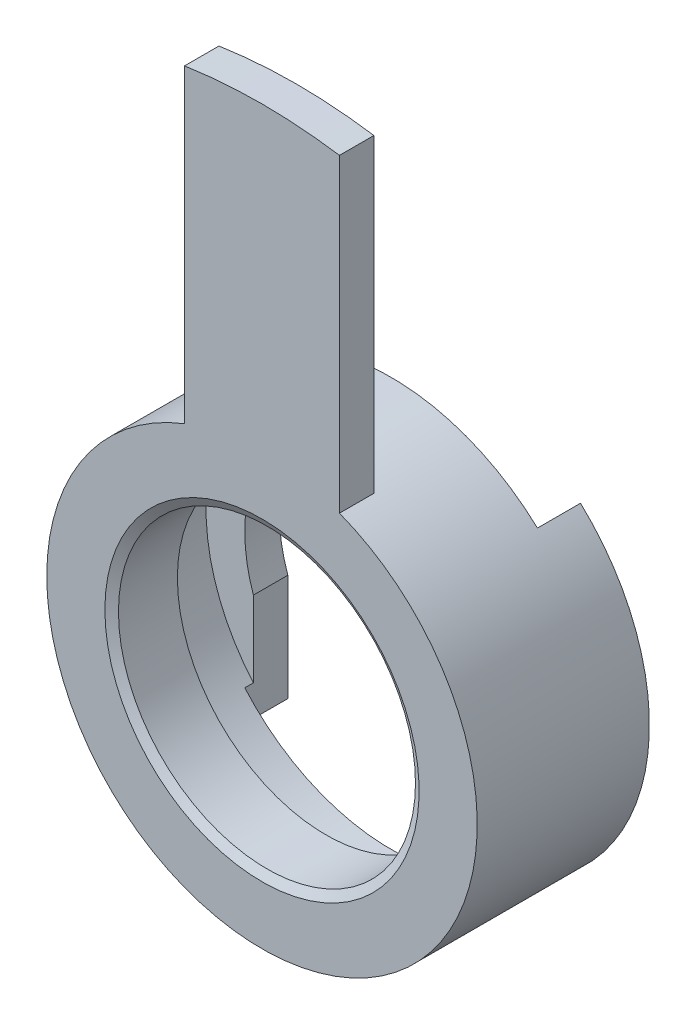
SolidWorks part; units mm, degrees
ref_plane "Спереди" through (0, 0, 0) normal (0, 0, 1) x (1, 0, 0)
ref_plane "Сверху" through (0, 0, 0) normal (0, 1, 0) x (1, 0, 0)
ref_plane "Справа" through (0, 0, 0) normal (1, 0, 0) x (0, 0, -1)
sketch "Эскиз1" plane through (0, 0, 0) normal (1, 0, 0) x (0, 0, -1)
  line L0 (0, 17.25) -> (0, 60)
  line L1 (0, 60) -> (4, 60)
  line L2 (4, 60) -> (4, 25)
  line L3 (4, 25) -> (20, 25)
  line L4 (20, 25) -> (20, 18)
  line L5 (20, 18) -> (16, 18)
  line L6 (16, 18) -> (16, 22.5)
  line L7 (16, 22.5) -> (8, 22.5)
  line L8 (8, 22.5) -> (8, 17.25)
  line L9 (8, 17.25) -> (0, 17.25)
  line L10 (0, 0) -> (25.7334, 0) construction
  dimension "D1" = 36
  dimension "D2" = 45
  dimension "D3" = 50
  dimension "D4" = 34.5
  dimension "D5" = 120
  dimension "D6" = 4
  dimension "D7" = 20
  dimension "D8" = 8
  dimension "D9" = 4
revolve "Повернуть1" add sketch "Эскиз1" angle 360 about L10
cosmetic thread "Условное изображение резьбы1" parameters "D2"=36
chamfer "Фаска1" distance 1 angle 30 2 edges at (17.25, 0, -8) (17.25, 0, 0)
sketch "Эскиз2" plane through (0, 0, -20) normal (0, 0, -1) x (-1, 0, 0)
  line L0 (-17, 18.3303) -> (-17, -18.3303)
  line L1 (17, 18.3303) -> (17, -18.3303)
  circle A0 centre (0, 0) radius 25 construction
  circle A1 centre (0, 0) radius 25 construction
  circle M1 centre (0, 0) radius 25
  circle M2 centre (0, 0) radius 18
  dimension "D2" = 34
extrude "Вырез-Вытянуть1" cut sketch "Эскиз2" against normal blind 5 contours L1 L0 M1 M2 | L1 L0 M2 M1
sketch "Эскиз3" plane through (0, 0, 0) normal (0, 0, 1) x (1, 0, 0)
  line L0 (-9, 59.3212) -> (-9, 23.3238)
  line L1 (9, 59.3212) -> (9, 23.3238)
  circle A0 centre (0, 0) radius 25
  circle A1 centre (0, 0) radius 25 construction
  circle A2 centre (0, 0) radius 60 construction
  circle M2 centre (0, 0) radius 60
  dimension "D1" = 18
extrude "Вырез-Вытянуть2" cut sketch "Эскиз3" against normal blind 5 contours A0 L0 L1 M2
